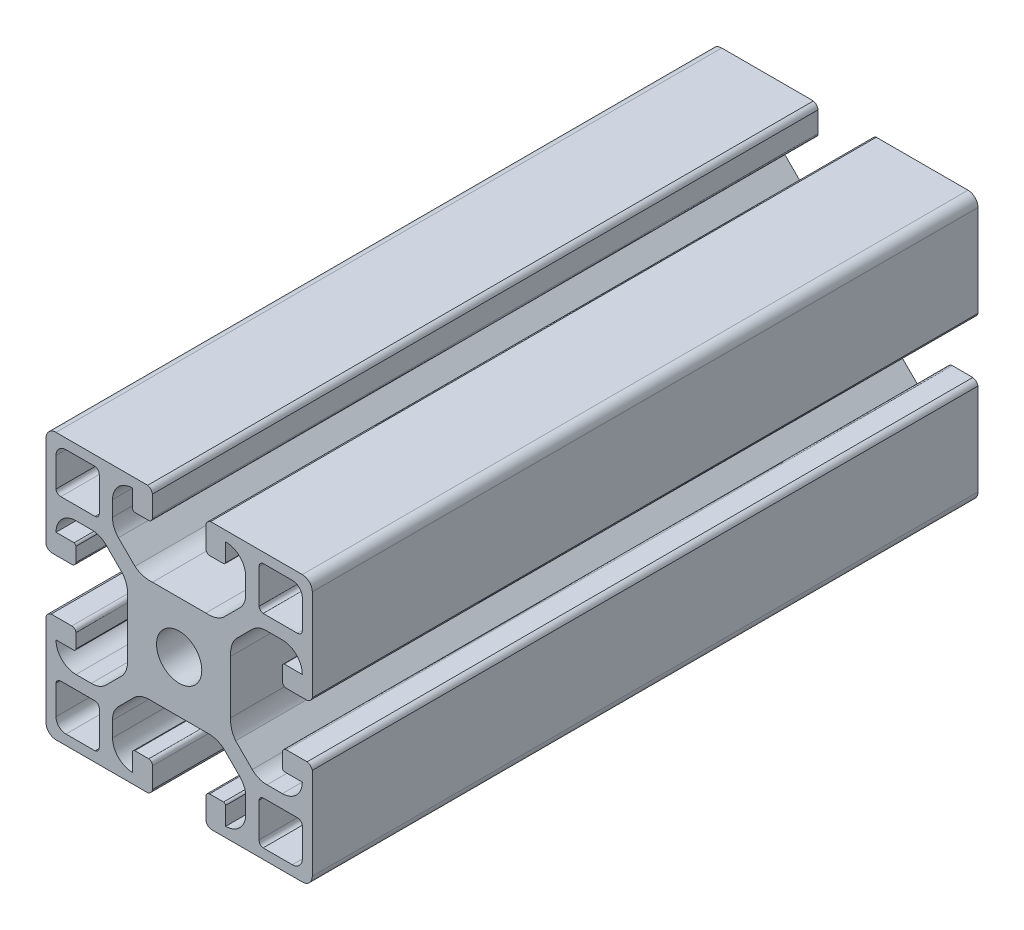
SolidWorks part; units mm, degrees
ref_plane "Alzado" through (0, 0, 0) normal (0, 0, 1) x (1, 0, 0)
ref_plane "Planta" through (0, 0, 0) normal (0, 1, 0) x (1, 0, 0)
ref_plane "Vista lateral" through (0, 0, 0) normal (1, 0, 0) x (0, 0, -1)
sketch "Croquis1" plane through (0, 0, 0) normal (0, 0, 1) x (1, 0, 0)
  line L9 (0, 18.5) -> (0, 4.7232)
  line L10 (0.7765, 4) -> (3.8765, 4)
  line L12 (12.25, -4.7232) -> (12.25, 4.7232)
  line L14 (4.5, 4.5616) -> (4.5, 6.6755)
  line L15 (4.2267, 7) -> (1.5, 7)
  line L17 (9.0164, 9.1211) -> (11.5076, 6.6299)
  line L18 (6.9331, 10) -> (4.5, 10)
  line L19 (40, -18.5) -> (40, -4.7232)
  line L20 (5.7166, 12) -> (7.3817, 12)
  line L21 (5.7166, 12) -> (2.23, 12)
  line L22 (1.5, 12.6183) -> (1.5, 17)
  line L23 (24.7232, 7.75) -> (15.2768, 7.75)
  line L24 (10.8789, 10.9836) -> (13.3701, 8.4924)
  line L25 (10, 13.0669) -> (10, 15.5)
  line L26 (13, 15.7733) -> (13, 18.5)
  line L27 (15.4384, 15.5) -> (13.3245, 15.5)
  line L28 (16, 19.2235) -> (16, 16.1235)
  line L29 (1.3293, 20) -> (15.2768, 20)
  line L30 (8, 14.2834) -> (8, 12.6183)
  line L31 (8, 14.2834) -> (8, 17.77)
  line L32 (7.3817, 18.5) -> (3, 18.5)
  line L33 (32.6183, 18.5) -> (37, 18.5)
  line L34 (32, 14.2834) -> (32, 17.77)
  line L35 (32, 14.2834) -> (32, 12.6183)
  line L36 (38.6707, 20) -> (24.7232, 20)
  line L37 (24, 19.2235) -> (24, 16.1235)
  line L38 (24.5616, 15.5) -> (26.6755, 15.5)
  line L39 (27, 15.7733) -> (27, 18.5)
  line L40 (30, 13.0669) -> (30, 15.5)
  line L41 (29.1211, 10.9836) -> (26.6299, 8.4924)
  line L42 (38.5, 12.6183) -> (38.5, 17)
  line L43 (34.2834, 12) -> (37.77, 12)
  line L44 (34.2834, 12) -> (32.6183, 12)
  line L45 (33.0669, 10) -> (35.5, 10)
  line L46 (30.9836, 9.1211) -> (28.4924, 6.6299)
  line L47 (35.7733, 7) -> (38.5, 7)
  line L48 (35.5, 4.5616) -> (35.5, 6.6755)
  line L49 (27.75, -4.7232) -> (27.75, 4.7232)
  line L51 (39.2235, 4) -> (36.1235, 4)
  line L52 (40, 18.5) -> (40, 4.7232)
  line L53 (39.2235, -4) -> (36.1235, -4)
  line L54 (35.5, -4.5616) -> (35.5, -6.6755)
  line L55 (35.7733, -7) -> (38.5, -7)
  line L56 (30.9836, -9.1211) -> (28.4924, -6.6299)
  line L57 (33.0669, -10) -> (35.5, -10)
  line L58 (34.2834, -12) -> (32.6183, -12)
  line L59 (34.2834, -12) -> (37.77, -12)
  line L60 (38.5, -12.6183) -> (38.5, -17)
  line L61 (29.1211, -10.9836) -> (26.6299, -8.4924)
  line L62 (30, -13.0669) -> (30, -15.5)
  line L63 (27, -15.7733) -> (27, -18.5)
  line L64 (24.5616, -15.5) -> (26.6755, -15.5)
  line L65 (24, -19.2235) -> (24, -16.1235)
  line L66 (38.6707, -20) -> (24.7232, -20)
  line L67 (32, -14.2834) -> (32, -12.6183)
  line L68 (32, -14.2834) -> (32, -17.77)
  line L69 (32.6183, -18.5) -> (37, -18.5)
  line L70 (7.3817, -18.5) -> (3, -18.5)
  line L71 (8, -14.2834) -> (8, -17.77)
  line L72 (8, -14.2834) -> (8, -12.6183)
  line L73 (1.3293, -20) -> (15.2768, -20)
  line L74 (16, -19.2235) -> (16, -16.1235)
  line L75 (15.4384, -15.5) -> (13.3245, -15.5)
  line L76 (13, -15.7733) -> (13, -18.5)
  line L77 (10, -13.0669) -> (10, -15.5)
  line L78 (10.8789, -10.9836) -> (13.3701, -8.4924)
  line L79 (24.7232, -7.75) -> (15.2768, -7.75)
  line L80 (1.5, -12.6183) -> (1.5, -17)
  line L81 (5.7166, -12) -> (2.23, -12)
  line L82 (5.7166, -12) -> (7.3817, -12)
  line L83 (6.9331, -10) -> (4.5, -10)
  line L84 (9.0164, -9.1211) -> (11.5076, -6.6299)
  line L85 (4.2267, -7) -> (1.5, -7)
  line L86 (4.5, -4.5616) -> (4.5, -6.6755)
  line L87 (0.7765, -4) -> (3.8765, -4)
  line L88 (0, -18.5) -> (0, -4.7232)
  arc A0 (4.5, 10) -> (1.5, 7) centre (4.5, 7) ccw
  arc A1 (10, 15.5) -> (13, 18.5) centre (13, 15.5) cw
  arc A2 (0, 18.5) -> (1.5, 20) centre (1.5, 18.5) cw
  arc A3 (1.5, 17) -> (3, 18.5) centre (3, 17) cw
  circle A4 centre (20, 0) radius 3.4
  arc A5 (38.5, 17) -> (37, 18.5) centre (37, 17) ccw
  arc A6 (40, 18.5) -> (38.5, 20) centre (38.5, 18.5) ccw
  arc A7 (30, 15.5) -> (27, 18.5) centre (27, 15.5) ccw
  arc A8 (35.5, 10) -> (38.5, 7) centre (35.5, 7) cw
  arc A9 (35.5, -10) -> (38.5, -7) centre (35.5, -7) ccw
  arc A10 (30, -15.5) -> (27, -18.5) centre (27, -15.5) cw
  arc A11 (40, -18.5) -> (38.5, -20) centre (38.5, -18.5) cw
  arc A12 (38.5, -17) -> (37, -18.5) centre (37, -17) cw
  arc A13 (1.5, -17) -> (3, -18.5) centre (3, -17) ccw
  arc A14 (0, -18.5) -> (1.5, -20) centre (1.5, -18.5) ccw
  arc A15 (10, -15.5) -> (13, -18.5) centre (13, -15.5) ccw
  arc A16 (4.5, -10) -> (1.5, -7) centre (4.5, -7) cw
  spline S0 degree 2 poles (6.7957, 10) (8.0801, 10.025) (9.0164, 9.1211) knots 0 0 0 1 1 1
  spline S1 degree 2 poles (11.5076, 6.6299) (12.3742, 5.4854) (12.25, 4) knots 0 0 0 1 1 1
  spline S2 degree 2 poles (0, 4.7232) (0.1682, 4.1542) (0.7765, 4) knots 0 0 0 1 1 1
  spline S3 degree 2 poles (3.8765, 4) (4.593, 4.0978) (4.5, 4.8884) knots 0 0 0 1 1 1
  spline S4 degree 2 poles (4.2267, 7) (4.4426, 6.908) (4.5, 6.6755) knots 0 0 0 1 1 1
  spline S5 degree 2 poles (13.3701, 8.4924) (14.5146, 7.6258) (16, 7.75) knots 0 0 0 1 1 1
  spline S6 degree 2 poles (10, 13.2043) (9.975, 11.9199) (10.8789, 10.9836) knots 0 0 0 1 1 1
  spline S7 degree 2 poles (13, 15.7733) (13.092, 15.5574) (13.3245, 15.5) knots 0 0 0 1 1 1
  spline S8 degree 2 poles (16, 16.1235) (15.9022, 15.407) (15.1116, 15.5) knots 0 0 0 1 1 1
  spline S9 degree 2 poles (15.2768, 20) (15.8458, 19.8318) (16, 19.2235) knots 0 0 0 1 1 1
  spline S10 degree 2 poles (1.5, 12.6183) (1.6133, 12.0451) (2.23, 12) knots 0 0 0 1 1 1
  spline S11 degree 2 poles (7.3817, 18.5) (7.9549, 18.3867) (8, 17.77) knots 0 0 0 1 1 1
  spline S12 degree 2 poles (7.3817, 12) (7.9101, 12.0752) (8, 12.6183) knots 0 0 0 1 1 1
  spline S13 degree 2 poles (32.6183, 12) (32.0899, 12.0752) (32, 12.6183) knots 0 0 0 1 1 1
  spline S14 degree 2 poles (32.6183, 18.5) (32.0451, 18.3867) (32, 17.77) knots 0 0 0 1 1 1
  spline S15 degree 2 poles (38.5, 12.6183) (38.3867, 12.0451) (37.77, 12) knots 0 0 0 1 1 1
  spline S16 degree 2 poles (24.7232, 20) (24.1542, 19.8318) (24, 19.2235) knots 0 0 0 1 1 1
  spline S17 degree 2 poles (24, 16.1235) (24.0978, 15.407) (24.8884, 15.5) knots 0 0 0 1 1 1
  spline S18 degree 2 poles (27, 15.7733) (26.908, 15.5574) (26.6755, 15.5) knots 0 0 0 1 1 1
  spline S19 degree 2 poles (30, 13.2043) (30.025, 11.9199) (29.1211, 10.9836) knots 0 0 0 1 1 1
  spline S20 degree 2 poles (26.6299, 8.4924) (25.4854, 7.6258) (24, 7.75) knots 0 0 0 1 1 1
  spline S21 degree 2 poles (35.7733, 7) (35.5574, 6.908) (35.5, 6.6755) knots 0 0 0 1 1 1
  spline S22 degree 2 poles (36.1235, 4) (35.407, 4.0978) (35.5, 4.8884) knots 0 0 0 1 1 1
  spline S23 degree 2 poles (40, 4.7232) (39.8318, 4.1542) (39.2235, 4) knots 0 0 0 1 1 1
  spline S24 degree 2 poles (28.4924, 6.6299) (27.6258, 5.4854) (27.75, 4) knots 0 0 0 1 1 1
  spline S25 degree 2 poles (33.2043, 10) (31.9199, 10.025) (30.9836, 9.1211) knots 0 0 0 1 1 1
  spline S26 degree 2 poles (33.2043, -10) (31.9199, -10.025) (30.9836, -9.1211) knots 0 0 0 1 1 1
  spline S27 degree 2 poles (28.4924, -6.6299) (27.6258, -5.4854) (27.75, -4) knots 0 0 0 1 1 1
  spline S28 degree 2 poles (40, -4.7232) (39.8318, -4.1542) (39.2235, -4) knots 0 0 0 1 1 1
  spline S29 degree 2 poles (36.1235, -4) (35.407, -4.0978) (35.5, -4.8884) knots 0 0 0 1 1 1
  spline S30 degree 2 poles (35.7733, -7) (35.5574, -6.908) (35.5, -6.6755) knots 0 0 0 1 1 1
  spline S31 degree 2 poles (26.6299, -8.4924) (25.4854, -7.6258) (24, -7.75) knots 0 0 0 1 1 1
  spline S32 degree 2 poles (30, -13.2043) (30.025, -11.9199) (29.1211, -10.9836) knots 0 0 0 1 1 1
  spline S33 degree 2 poles (27, -15.7733) (26.908, -15.5574) (26.6755, -15.5) knots 0 0 0 1 1 1
  spline S34 degree 2 poles (24, -16.1235) (24.0978, -15.407) (24.8884, -15.5) knots 0 0 0 1 1 1
  spline S35 degree 2 poles (24.7232, -20) (24.1542, -19.8318) (24, -19.2235) knots 0 0 0 1 1 1
  spline S36 degree 2 poles (38.5, -12.6183) (38.3867, -12.0451) (37.77, -12) knots 0 0 0 1 1 1
  spline S37 degree 2 poles (32.6183, -18.5) (32.0451, -18.3867) (32, -17.77) knots 0 0 0 1 1 1
  spline S38 degree 2 poles (32.6183, -12) (32.0899, -12.0752) (32, -12.6183) knots 0 0 0 1 1 1
  spline S39 degree 2 poles (7.3817, -12) (7.9101, -12.0752) (8, -12.6183) knots 0 0 0 1 1 1
  spline S40 degree 2 poles (7.3817, -18.5) (7.9549, -18.3867) (8, -17.77) knots 0 0 0 1 1 1
  spline S41 degree 2 poles (1.5, -12.6183) (1.6133, -12.0451) (2.23, -12) knots 0 0 0 1 1 1
  spline S42 degree 2 poles (15.2768, -20) (15.8458, -19.8318) (16, -19.2235) knots 0 0 0 1 1 1
  spline S43 degree 2 poles (16, -16.1235) (15.9022, -15.407) (15.1116, -15.5) knots 0 0 0 1 1 1
  spline S44 degree 2 poles (13, -15.7733) (13.092, -15.5574) (13.3245, -15.5) knots 0 0 0 1 1 1
  spline S45 degree 2 poles (10, -13.2043) (9.975, -11.9199) (10.8789, -10.9836) knots 0 0 0 1 1 1
  spline S46 degree 2 poles (13.3701, -8.4924) (14.5146, -7.6258) (16, -7.75) knots 0 0 0 1 1 1
  spline S47 degree 2 poles (4.2267, -7) (4.4426, -6.908) (4.5, -6.6755) knots 0 0 0 1 1 1
  spline S48 degree 2 poles (3.8765, -4) (4.593, -4.0978) (4.5, -4.8884) knots 0 0 0 1 1 1
  spline S49 degree 2 poles (0, -4.7232) (0.1682, -4.1542) (0.7765, -4) knots 0 0 0 1 1 1
  spline S50 degree 2 poles (11.5076, -6.6299) (12.3742, -5.4854) (12.25, -4) knots 0 0 0 1 1 1
  spline S51 degree 2 poles (6.7957, -10) (8.0801, -10.025) (9.0164, -9.1211) knots 0 0 0 1 1 1
extrude "Saliente-Extruir1" add sketch "Croquis1" along normal blind 100 contours S51 L83 A16 L85 S47 L86 S48 L87 S49 L88 A14 L73 S42 L74 S43 L75 S44 L76 A15 L77 S45 L78 S46 L79 S31 L61 S32 L62 A10 L63 S33 L64 S34 L65 S35 L66 A11 L19 S28 L53 S29 L54 S30
